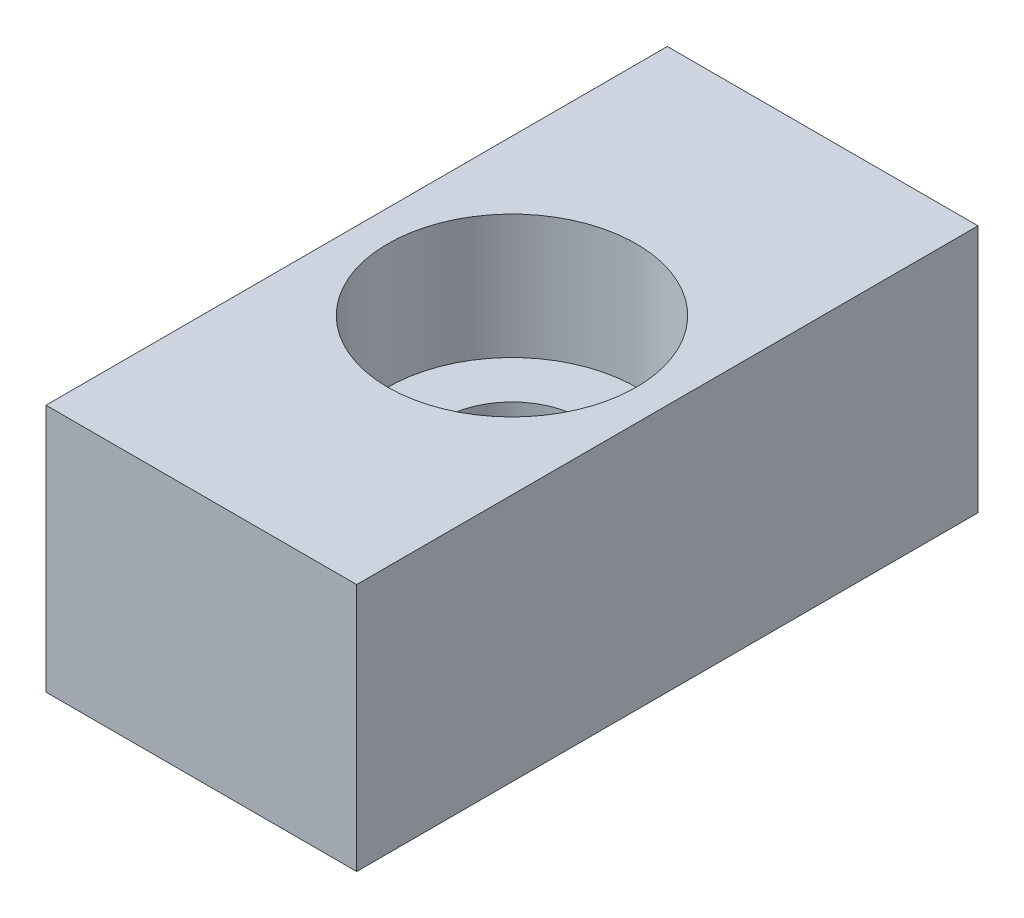
SolidWorks part; units mm, degrees
ref_plane "Front Plane" through (0, 0, 0) normal (0, 0, 1) x (1, 0, 0)
ref_plane "Top Plane" through (0, 0, 0) normal (0, 1, 0) x (1, 0, 0)
ref_plane "Right Plane" through (0, 0, 0) normal (1, 0, 0) x (0, 0, -1)
sketch "Sketch1" plane through (0, 0, 0) normal (0, 1, 0) x (1, 0, 0)
  line L1 (-5, -10) -> (5, -10)
  line L2 (-5, -10) -> (-5, 10)
  line L3 (-5, 10) -> (5, 10)
  line L4 (5, -10) -> (5, 10)
  line L5 (-5, -10) -> (5, 10) construction
  line L6 (-5, 10) -> (5, -10) construction
  circle A0 centre (0, 0) radius 2.25
  dimension "D1" = 4.5
  dimension "D2" = 20
  dimension "D3" = 10
extrude "Boss-Extrude1" add sketch "Sketch1" along normal blind 4
sketch "Sketch2" plane through (0, 4, 0) normal (0, 1, 0) x (1, 0, 0)
  line L1 (-5, 10) -> (5, 10)
  line L2 (-5, 10) -> (-5, -10)
  line L3 (-5, -10) -> (5, -10)
  line L4 (5, 10) -> (5, -10)
  circle A0 centre (0, 0) radius 4
  dimension "D1" = 8
extrude "Boss-Extrude2" add sketch "Sketch2" along normal blind 4
